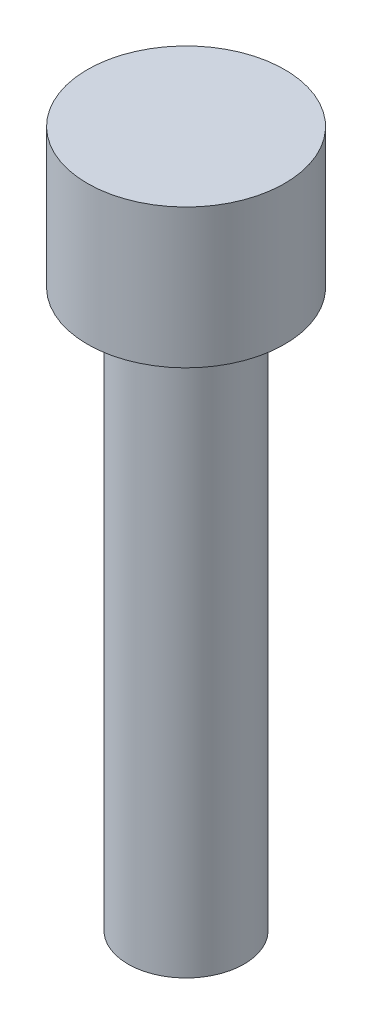
SolidWorks part; units mm, degrees
ref_plane "Front Plane" through (0, 0, 0) normal (0, 0, 1) x (1, 0, 0)
ref_plane "Top Plane" through (0, 0, 0) normal (0, 1, 0) x (1, 0, 0)
ref_plane "Right Plane" through (0, 0, 0) normal (1, 0, 0) x (0, 0, -1)
sketch "Sketch1" plane through (0, 0, 0) normal (0, 1, 0) x (1, 0, 0)
  circle A0 centre (0, 0) radius 2.5
  dimension "D1" = 5
extrude "Boss-Extrude1" add sketch "Sketch1" along normal blind 24
sketch "Sketch2" plane through (0, 24, 0) normal (0, 1, 0) x (1, 0, 0)
  circle A0 centre (0, 0) radius 4.25
  dimension "D1" = 8.5
extrude "Boss-Extrude2" add sketch "Sketch2" along normal blind 6
